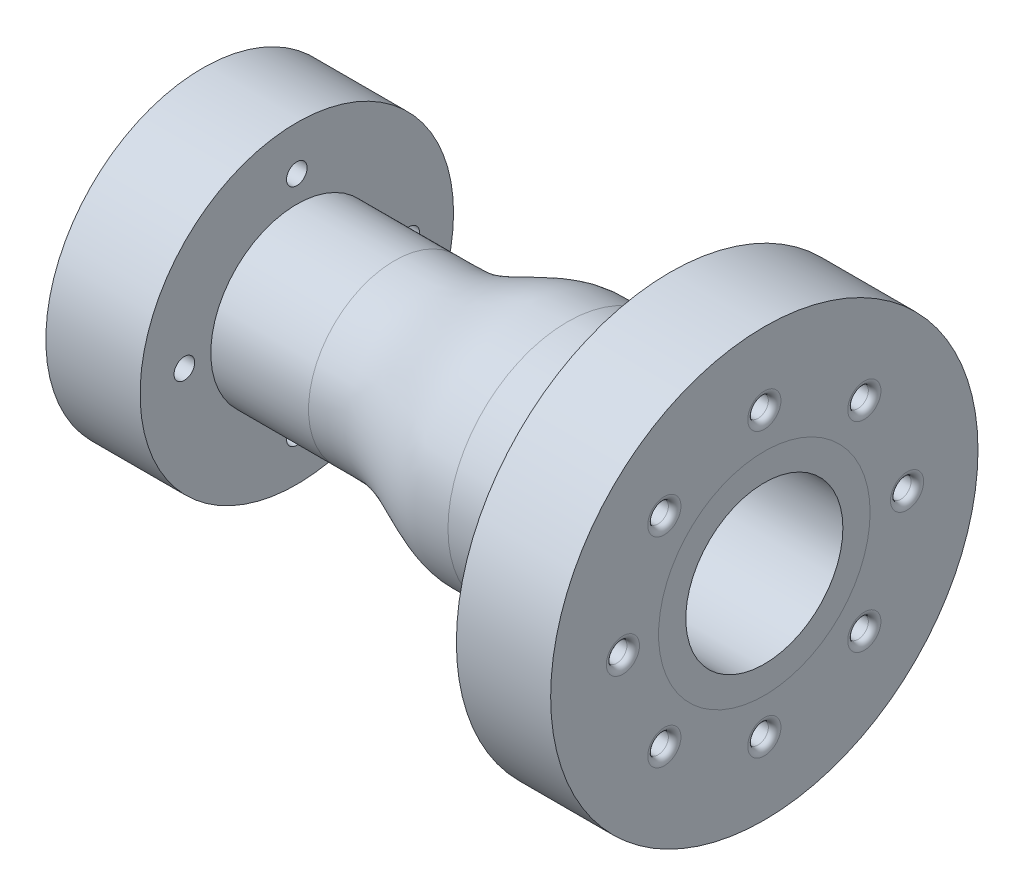
SolidWorks part; units mm, degrees
material "Cast Alloy Steel"
ref_plane "Front Plane" through (0, 0, 0) normal (0, 0, 1) x (1, 0, 0)
ref_plane "Top Plane" through (0, 0, 0) normal (0, 1, 0) x (1, 0, 0)
ref_plane "Right Plane" through (0, 0, 0) normal (1, 0, 0) x (0, 0, -1)
sketch "Sketch2" plane through (0, 0, 0) normal (0, 0, 1) x (1, 0, 0)
  line L0 (341.7, 0) -> (0, 0) construction
  line L4 (397.9, 63.5) -> (397.9, 172.72)
  line L5 (20, 126.6825) -> (-56.2, 126.6825)
  line L6 (397.9, 172.72) -> (321.7, 172.72)
  line L8 (-56.2, 126.6825) -> (-56.2, 36.5125)
  line L9 (321.7, 172.72) -> (321.7, 96.52)
  line L10 (20, 126.6825) -> (20, 69.5325)
  line L11 (99, 69.5325) -> (20, 69.5325)
  line L12 (238.7, 63.5) -> (321.7, 63.5) construction
  line L13 (238.7, 96.52) -> (321.7, 96.52)
  line L14 (238.7, 63.5) -> (397.9, 63.5)
  line L15 (99, 36.5125) -> (-56.2, 36.5125)
  line L16 (99, 36.5125) -> (20, 36.5125) construction
  spline S1 degree 3 poles (238.7, 96.52) (235.5542, 96.52) (231.8676, 96.52) (227.493, 96.52) (225.7234, 96.52) (223.8064, 96.52) (222.0369, 96.52) (220.1199, 96.5199) (218.3504, 96.5204) (216.4362, 96.5188) (214.6713, 96.5253) (212.7611, 96.4693) (210.998, 96.3644) (209.0881, 96.1941) (207.3251, 95.9862) (205.4153, 95.7081) (203.6525, 95.404) (201.743, 95.0256) (199.9803, 94.6326) (198.071, 94.1621) (196.3085, 93.6881) (194.3993, 93.1344) (192.637, 92.5879) (190.7279, 91.9604) (188.9657, 91.3504) (187.0568, 90.659) (185.2947, 89.9948) (183.3858, 89.25) (181.6238, 88.5415) (179.715, 87.7542) (177.9531, 87.0115) (176.0443, 86.1928) (173.5953, 85.1274) (170.4623, 83.7431) (167.4762, 82.4156) (165.0248, 81.332) (163.2593, 80.5569) (161.3467, 79.7264) (159.5811, 78.9705) (157.6684, 78.1665) (155.9029, 77.4404) (153.9901, 76.6743) (152.2245, 75.9884) (150.3116, 75.2713) (148.5459, 74.6355) (146.6329, 73.978) (144.8671, 73.4021) (142.4203, 72.6506) (139.9691, 71.9684) (137.5086, 71.3706) (135.5952, 70.9514) (133.8288, 70.6083) (131.9153, 70.2864) (130.1487, 70.0369) (128.235, 69.8202) (126.4683, 69.6712) (124.7896, 69.58) (123.4438, 69.5395) (122.4205, 69.5315) (121.678, 69.5326) (120.6018, 69.5323) (119.2022, 69.5326) (117.2852, 69.5325) (115.5156, 69.5325) (110.6003, 69.5325) (105.1442, 69.5325) (100.2288, 69.5325) (99, 69.5325) knots 0 0 0 0 0.06541 0.076652 0.09096 0.102202 0.116511 0.127753 0.142061 0.153304 0.167554 0.178755 0.193031 0.204272 0.218621 0.229935 0.244395 0.25581 0.270409 0.28194 0.296695 0.308353 0.323271 0.335057 0.350135 0.362043 0.377271 0.389288 0.404646 0.416757 0.43222 0.444402 0.459941 0.487751 0.515621 0.527887 0.54348 0.555711 0.571243 0.583412 0.598851 0.610936 0.626254 0.638235 0.65341 0.665273 0.680292 0.692028 0.718491 0.733185 0.74467 0.759216 0.770593 0.785014 0.796305 0.810635 0.821871 0.831257 0.838628 0.843146 0.846696 0.861005 0.872247 0.886555 0.897798 0.974449 1 1 1 1 weights 0.576132 0.576132 0.576132 0.576132 0.576132 0.576132 0.576132 0.576132 0.576132 0.576132 0.576132 0.576132 0.576132 0.576132 0.576132 0.576132 0.576132 0.576132 0.576132 0.576132 0.576132 0.576132 0.576132 0.576132 0.576132 0.576132 0.576132 0.576132 0.576132 0.576132 0.576132 0.576132 0.576132 0.576132 0.576132 0.576132 0.576132 0.576132 0.576132 0.576132 0.576132 0.576132 0.576132 0.576132 0.576132 0.576132 0.576132 0.576132 0.576132 0.576132 0.576132 0.576132 0.576132 0.576132 0.576132 0.576132 0.576132 0.576132 0.576132 0.576132 0.576132 0.576132 0.576132 0.576132 0.576132 0.576132 0.576132 0.576132
  spline S2 degree 1 poles (238.7, 63.5) (99, 36.5125) knots 0 0 1 1 construction
  spline S3 degree 3 poles (238.7, 63.5) (237.197, 63.5) (234.1911, 63.5) (230.4339, 63.5) (227.4277, 63.5) (225.1739, 63.5) (222.9178, 63.5) (221.0429, 63.4999) (219.5304, 63.5001) (218.4155, 63.5003) (217.3142, 63.4992) (216.0437, 63.501) (215.186, 63.5005) (214.7714, 63.4933) (214.2525, 63.4754) (213.5579, 63.4377) (212.672, 63.3659) (211.172, 63.1914) (209.1633, 62.8581) (206.518, 62.2577) (203.647, 61.4511) (200.5615, 60.4409) (196.1795, 58.8367) (190.2299, 56.3871) (182.3724, 52.9027) (173.7449, 49.0711) (165.8008, 45.7804) (158.893, 43.2438) (153.4089, 41.4413) (147.5983, 39.7991) (141.4488, 38.3906) (136.0423, 37.4812) (131.5702, 36.9579) (128.7095, 36.7241) (126.402, 36.5998) (124.9605, 36.5479) (123.7385, 36.5227) (122.8844, 36.5138) (122.222, 36.5121) (121.7912, 36.5124) (121.4549, 36.5126) (120.9876, 36.5124) (120.2265, 36.5124) (119.2869, 36.5125) (118.164, 36.5125) (116.6593, 36.5125) (114.7811, 36.5125) (112.5266, 36.5125) (110.2722, 36.5125) (107.2662, 36.5125) (103.5088, 36.5125) (100.5029, 36.5125) (99, 36.5125) knots 0 0 0 0 0.03125 0.0625 0.078125 0.09375 0.109375 0.125 0.132812 0.140625 0.148438 0.15625 0.164062 0.171875 0.179688 0.1875 0.203125 0.21875 0.25 0.28125 0.3125 0.34375 0.375 0.4375 0.5 0.5625 0.625 0.65625 0.6875 0.71875 0.75 0.78125 0.796875 0.8125 0.820312 0.828125 0.832031 0.835938 0.839844 0.841797 0.84375 0.847656 0.851562 0.859375 0.867188 0.875 0.890625 0.90625 0.921875 0.9375 0.96875 1 1 1 1
  dimension "D1" = 76.2
  dimension "D3" = 76.2
  dimension "D4" = 63.5
  dimension "D2" = 33.02
revolve "Revolve1" add sketch "Sketch2" angle 360 about L0
sketch "Sketch3" plane through (397.9, 0, 0) normal (1, 0, 0) x (0, 0, -1)
  circle A0 centre (0, -120.65) radius 11.175
  circle A1 centre (0, 0) radius 120.65 construction
  dimension "D1" = 22.35
  dimension "D2" = 241.3
extrude "Cut-Extrude1" [suppressed] cut sketch "Sketch3" against normal up to surface (20 mm away)
sketch "Sketch4" plane through (-56.2, 0, 0) normal (-1, 0, 0) x (0, 0, 1)
  circle A0 centre (0, 0) radius 95.25 construction
  circle A1 centre (0, 95.25) radius 9.5
  dimension "D1" = 190.5
  dimension "D2" = 19
extrude "Cut-Extrude2" [suppressed] cut sketch "Sketch4" against normal up to surface (20 mm away)
pattern_circular "CirPattern1" [suppressed] count 4 over 360 about axis through (341.7, 0, 0) along (-1, 0, 0)
sketch "Sketch5" plane through (397.9, 0, 0) normal (1, 0, 0) x (0, 0, -1)
  circle A0 centre (0, 0) radius 85.5
  dimension "D1" = 171
split line "Split Line1"
hole_wizard "5/8 Clearance Hole1" positions "Sketch6" profile "Sketch7" hole size "5/8" standard "Ansi Inch"
sketch "Sketch6" plane through (-56.2, -86.9453, 61.2299) normal (-1, 0, 0) x (0, 0, 1)
  line L0 (-61.2299, 86.9453) -> (160.2598, 86.9453) construction
  line L1 (-61.2299, 86.9453) -> (-61.2299, 296.6144) construction
  line L2 (-61.2299, 86.9453) -> (-291.9631, 86.9453) construction
  line L3 (-61.2299, 86.9453) -> (-61.2299, -121.1078) construction
  circle A0 centre (-61.2299, 86.9453) radius 90.9114 construction
  point P0 (-61.2299, 177.798)
  point P1 (29.6815, 86.9453)
  point P2 (-61.2299, -3.9661)
  point P3 (-152.1413, 86.9453)
  point P14 (-61.2299, 177.798)
  point P15 (0, 0)
  point P16 (0, 0)
sketch "Sketch7" plane through (-56.2, 90.8528, 0) normal (0, 1, 0) x (0, 0, 1)
  line L0 (0, 0) -> (0, 76.2)
  line L1 (0, 76.2) -> (8.3337, 76.2)
  line L2 (8.3337, 76.2) -> (8.3337, 0)
  line L3 (8.3337, 0) -> (0, 0)
  line L4 (0, -6.35) -> (0, 107.95) construction
  dimension "Thru Hole Dia." = 16.6675
  dimension "Thru Hole Depth" = 76.2
hole_wizard "CSK for 5/8 Flat Head Machine Screw (100)1" positions "Sketch10" profile "Sketch11" countersink size "5/8" standard "Ansi Inch"
sketch "Sketch10" plane through (321.7, -86.9453, 61.2299) normal (-1, 0, 0) x (0, 0, 1)
  line L0 (-61.2299, 86.9453) -> (-61.2299, 353.2126) construction
  line L1 (-61.2299, 86.9453) -> (208.6165, 86.9453) construction
  line L2 (-61.2299, 86.9453) -> (-335.3638, 86.9453) construction
  line L3 (-61.2299, 86.9453) -> (-61.2299, -193.2291) construction
  line L7 (-61.2299, 86.9453) -> (113.4341, 261.6093) construction
  line L8 (-61.2299, 86.9453) -> (150.6399, -124.9245) construction
  line L9 (-61.2299, 86.9453) -> (-186.2909, 212.0063) construction
  line L10 (-61.2299, 86.9453) -> (-176.5965, -28.4213) construction
  circle A0 centre (-61.2299, 86.9453) radius 114.3 construction
  point P0 (-61.2299, 201.2453)
  point P1 (-176.5965, 86.9453)
  point P2 (-142.0522, 167.7676)
  point P3 (19.5924, 167.7676)
  point P4 (53.0701, 86.9453)
  point P5 (19.5924, 6.123)
  point P6 (-61.2299, -27.4065)
  point P7 (-142.0522, 6.123)
sketch "Sketch11" plane through (321.7, 114.3, 0) normal (0, 1, 0) x (0, 0, 1)
  line L0 (0, 0) -> (0, 76.2)
  line L1 (0, 76.2) -> (8.3337, 76.2)
  line L2 (8.3337, 76.2) -> (8.3337, 6.5623)
  line L3 (8.3337, 6.5623) -> (16.1544, 0)
  line L4 (16.1544, 0) -> (0, 0)
  line L5 (-8.3337, 6.5623) -> (-16.1544, 0) construction
  line L6 (0, -6.35) -> (0, 107.95) construction
  dimension "Thru Hole Dia." = 16.6675
  dimension "Thru Hole Depth" = 76.2
  dimension "Near C'Sink Dia." = 32.3088
  dimension "Near C'Sink Angle" = 100
hole_wizard "CSK for 5/8 Flat Head Machine Screw (100)2" [suppressed] positions "Sketch12" profile "Sketch13" countersink size "5/8" standard "Ansi Inch"
sketch "Sketch12" plane through (321.7, -86.9453, 61.2299) normal (-1, 0, 0) x (0, 0, 1)
  point P0 (-64.3378, 197.2771)
  point P1 (39.851, 49.4978)
  point P2 (-73.6499, -26.8437)
  point P3 (-171.7422, 70.605)
sketch "Sketch13" plane through (321.7, 110.3318, -3.1079) normal (0, 1, 0) x (0, 0, 1)
  line L0 (0, 0) -> (0, 20)
  line L1 (0, 20) -> (8.3337, 20)
  line L2 (8.3337, 20) -> (8.3337, 6.5623)
  line L3 (8.3337, 6.5623) -> (16.1544, 0)
  line L4 (16.1544, 0) -> (0, 0)
  line L5 (-8.3337, 6.5623) -> (-16.1544, 0) construction
  line L6 (0, -6.35) -> (0, 107.95) construction
  dimension "Thru Hole Dia." = 16.6675
  dimension "Thru Hole Depth" = 20
  dimension "Near C'Sink Dia." = 32.3088
  dimension "Near C'Sink Angle" = 100
fillet "Fillet1" radius 5.08 8 edges at (397.9, -80.8223, -72.4886) (397.9, 0, -107.0328) (397.9, 80.8223, -72.4886) (397.9, 114.3, 8.3337) (397.9, 80.8223, 89.156) (397.9, 0, 122.6337) (397.9, -80.8223, 89.156) (397.9, -114.3518, 8.3337)
fillet "Fillet2" radius 5.08 4 edges at (-56.2, 0, -82.5776) (-56.2, 90.8528, 8.3337) (-56.2, 0, 99.2451) (-56.2, -90.9114, 8.3337)
